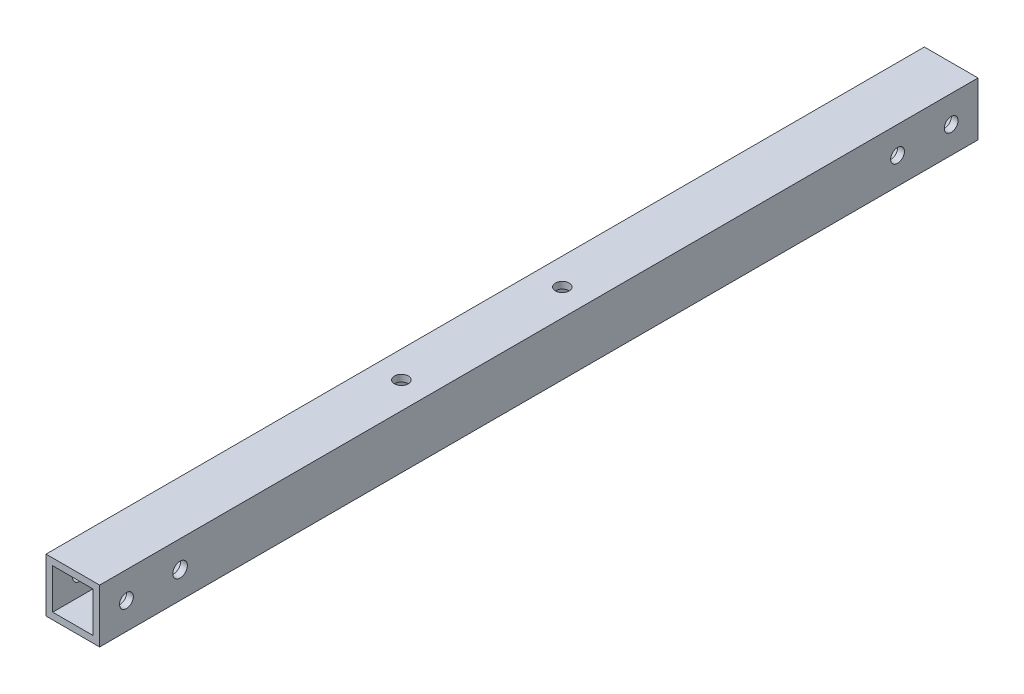
SolidWorks part; units mm, degrees
ref_plane "Front Plane" through (0, 0, 0) normal (0, 0, 1) x (1, 0, 0)
ref_plane "Top Plane" through (0, 0, 0) normal (0, 1, 0) x (1, 0, 0)
ref_plane "Right Plane" through (0, 0, 0) normal (1, 0, 0) x (0, 0, -1)
sketch "Sketch1" plane through (0, 0, 0) normal (0, 0, 1) x (1, 0, 0)
  line L0 (-9.525, 9.525) -> (9.525, 9.525)
  line L1 (-12.7, -12.7) -> (12.7, -12.7)
  line L2 (-12.7, -12.7) -> (-12.7, 12.7)
  line L3 (-12.7, 12.7) -> (12.7, 12.7)
  line L4 (12.7, -12.7) -> (12.7, 12.7)
  line L5 (-12.7, -12.7) -> (12.7, 12.7) construction
  line L6 (-12.7, 12.7) -> (12.7, -12.7) construction
  line L7 (9.525, -9.525) -> (9.525, 9.525)
  line L8 (-9.525, -9.525) -> (9.525, -9.525)
  line L9 (-9.525, -9.525) -> (-9.525, 9.525)
  point P0 (0, 0)
  dimension "D1" = 25.4
  dimension "D2" = 25.4
  dimension "D3" = 3.175
extrude "Boss-Extrude1" add sketch "Sketch1" along normal blind 415.925
hole_wizard "F (0.257) Diameter Hole1" positions "Sketch2" profile "Sketch3" hole size "F" standard "ANSI Inch" end condition through all
sketch "Sketch2" plane through (12.7, 0, 0) normal (1, 0, 0) x (0, 0, -1)
  line L0 (-415.925, -12.7) -> (-415.925, 12.7) construction
  line L1 (0, -12.7) -> (0, 12.7) construction
  point P0 (-403.225, 0)
  point P2 (-12.7, 0)
  point P4 (-38.1, 0)
  dimension "D1" = 12.7
  dimension "D2" = 25.4
  dimension "D3" = 12.7
sketch "Sketch3" plane through (12.7, 0, 403.225) normal (0, 1, 0) x (0, 0, -1)
  line L0 (0, 0) -> (0, 25.4)
  line L1 (0, 25.4) -> (3.2639, 25.4)
  line L2 (3.2639, 25.4) -> (3.2639, 0)
  line L5 (3.2639, 0) -> (0, 0)
  line L11 (0, -6.35) -> (0, 107.95) construction
  dimension "Thru Hole Dia." = 6.5278
  dimension "Thru Hole Depth" = 25.4
hole_wizard "I (0.272) Diameter Hole1" positions "Sketch4" profile "Sketch5" hole size "I" standard "ANSI Inch" end condition through all
sketch "Sketch4" plane through (12.7, 0, 0) normal (1, 0, 0) x (0, 0, -1)
  line L0 (-415.925, -12.7) -> (-415.925, 12.7) construction
  point P0 (-377.825, 0)
  dimension "D1" = 38.1
sketch "Sketch5" plane through (12.7, 0, 377.825) normal (0, 1, 0) x (0, 0, -1)
  line L0 (0, 0) -> (0, 25.4)
  line L1 (0, 25.4) -> (3.4544, 25.4)
  line L2 (3.4544, 25.4) -> (3.4544, 0)
  line L5 (3.4544, 0) -> (0, 0)
  line L11 (0, -6.35) -> (0, 107.95) construction
  dimension "Thru Hole Dia." = 6.9088
  dimension "Thru Hole Depth" = 25.4
hole_wizard "F (0.257) Diameter Hole2" positions "Sketch6" profile "Sketch7" hole size "F" standard "ANSI Inch" end condition through all
sketch "Sketch6" plane through (0, 12.7, 0) normal (0, 1, 0) x (1, 0, 0)
  line L0 (12.7, 0) -> (-12.7, 0) construction
  line L2 (-12.7, -196.85) -> (12.7, -196.85)
  line L3 (-12.7, -196.85) -> (-12.7, -222.25)
  line L4 (-12.7, -222.25) -> (12.7, -222.25)
  line L5 (12.7, -196.85) -> (12.7, -222.25)
  line L6 (-12.7, -415.925) -> (-12.7, 0) construction
  line L7 (12.7, -415.925) -> (12.7, 0) construction
  point P0 (0, -184.15)
  point P103 (0, -260.35)
  dimension "D1" = 184.15
  dimension "D2" = 12.7
  dimension "D3" = 25.4
  dimension "D4" = 38.1
sketch "Sketch7" plane through (0, 12.7, 184.15) normal (1, 0, 0) x (0, 0, 1)
  line L0 (0, 0) -> (0, 25.4)
  line L1 (0, 25.4) -> (3.2639, 25.4)
  line L2 (3.2639, 25.4) -> (3.2639, 0)
  line L5 (3.2639, 0) -> (0, 0)
  line L11 (0, -6.35) -> (0, 107.95) construction
  dimension "Thru Hole Dia." = 6.5278
  dimension "Thru Hole Depth" = 25.4
